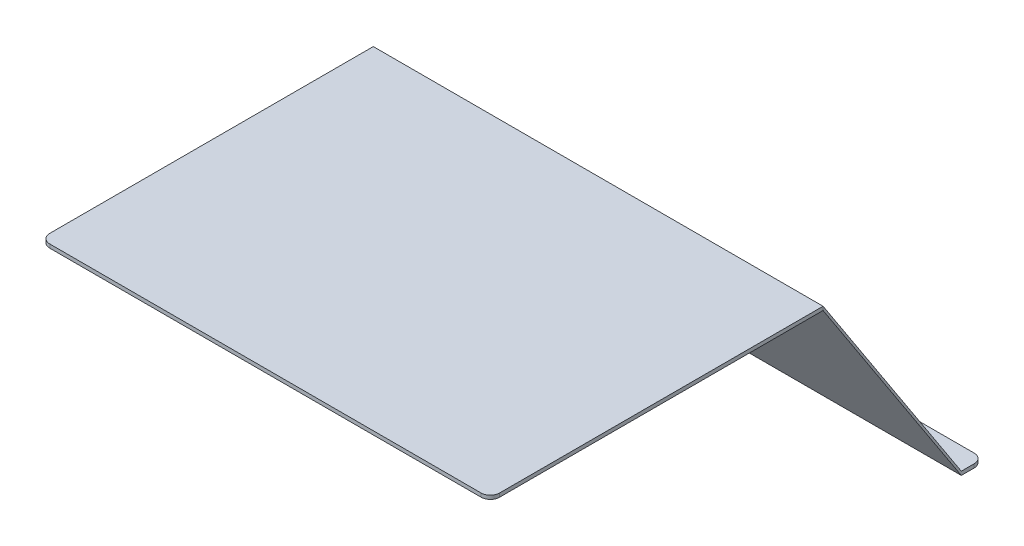
SolidWorks part; units mm, degrees
material "6061-T6 (SS)"
ref_plane "Front Plane" through (0, 0, 0) normal (0, 0, 1) x (1, 0, 0)
ref_plane "Top Plane" through (0, 0, 0) normal (0, 1, 0) x (1, 0, 0)
ref_plane "Right Plane" through (0, 0, 0) normal (1, 0, 0) x (0, 0, -1)
sketch "Sketch2" plane through (0, 0, 0) normal (1, 0, 0) x (0, 0, -1)
  line L1 (0, 0) -> (361, 0)
  line L2 (0, 0) -> (0, 4)
  line L3 (0, 4) -> (361, 4)
  line L4 (361, 0) -> (361, 4)
  dimension "D1" = 4
  dimension "D2" = 361
extrude "Boss-Extrude1" add sketch "Sketch2" along normal blind 488
sketch "Sketch3" plane through (488, 0, 0) normal (1, 0, 0) x (0, 0, -1)
  line L9 (361, 4) -> (511, -226)
  line L22 (511, -226) -> (511, -230)
  line L23 (511, -230) -> (361, 0)
  line L24 (361, 0) -> (361, 4)
  dimension "D1" = 4
  dimension "D2" = 150
  dimension "D3" = 234
extrude "Boss-Extrude2" add sketch "Sketch3" against normal blind 488 separate body
sketch "Sketch4" plane through (0, 0, -511) normal (0, 0, -1) x (-1, 0, 0)
  line L1 (0, -226) -> (-488, -226)
  line L2 (0, -226) -> (0, -230)
  line L3 (0, -230) -> (-488, -230)
  line L4 (-488, -226) -> (-488, -230)
extrude "Boss-Extrude3" add sketch "Sketch4" along normal blind 24
fillet "Fillet2" radius 10 2 edges at (488, -228, -535) (0, -228, -535)
fillet "Fillet3" radius 10 2 edges at (0, 2, 0) (488, 2, 0)
